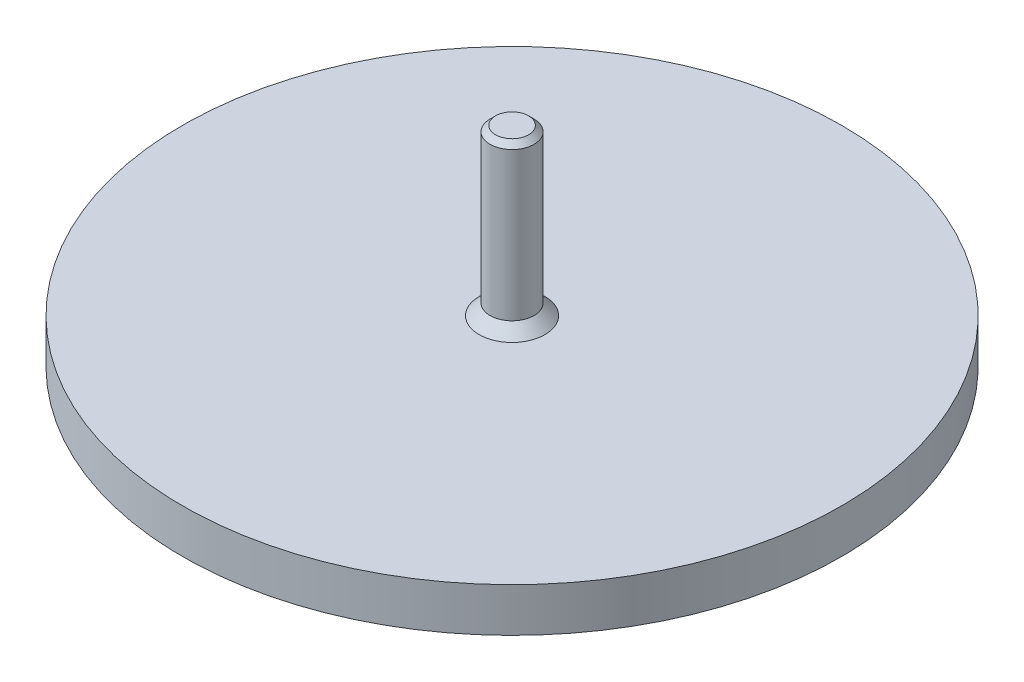
SolidWorks part; units mm, degrees
ref_plane "Face" through (0, 0, 0) normal (0, 0, 1) x (1, 0, 0)
ref_plane "Dessus" through (0, 0, 0) normal (0, 1, 0) x (1, 0, 0)
ref_plane "Droite" through (0, 0, 0) normal (1, 0, 0) x (0, 0, -1)
sketch "Esquisse1" plane through (0, 0, 0) normal (0, 0, 1) x (1, 0, 0)
  line L0 (0, 0) -> (0, 95.3652) construction
  line L1 (0, 0) -> (-30, 0)
  line L2 (-30, 4) -> (-2, 4)
  line L3 (-2, 4) -> (-2, 19)
  line L4 (-2, 19) -> (0, 19)
  line L5 (0, 0) -> (0, 19)
  line L7 (-30, 0) -> (-30, 4)
  line L8 (-30, 4) -> (-30, 0) construction
  line L9 (0, 2) -> (-30, 2) construction
  dimension "D1" = 2
  dimension "D2" = 2
  dimension "D3" = 15
  dimension "D4" = 30
revolve "Révolution1" add sketch "Esquisse1" angle 360 about L0
chamfer "Chanfrein1" distance 1 angle 45 1 edges at (0, 4, -2)
chamfer "Chanfrein2" distance 0.5 angle 45 1 edges at (0, 19, -2)
